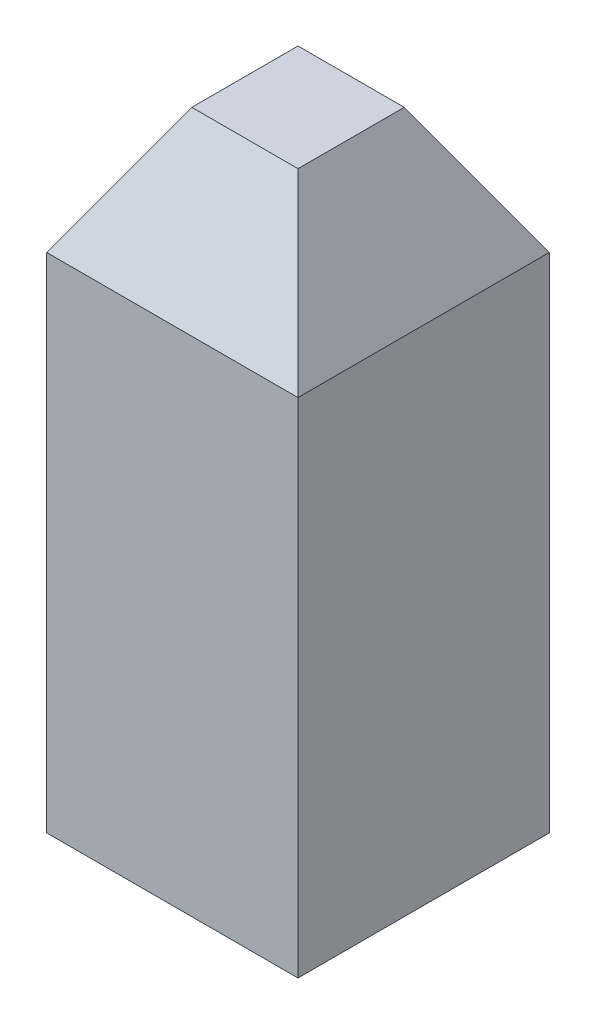
SolidWorks part; units mm, degrees
ref_plane "Front Plane" through (0, 0, 0) normal (0, 0, 1) x (1, 0, 0)
ref_plane "Top Plane" through (0, 0, 0) normal (0, 1, 0) x (1, 0, 0)
ref_plane "Right Plane" through (0, 0, 0) normal (1, 0, 0) x (0, 0, -1)
sketch "Sketch1" plane through (0, 0, 0) normal (0, 1, 0) x (1, 0, 0)
  line L1 (-0.25, -0.25) -> (0.25, -0.25)
  line L2 (-0.25, -0.25) -> (-0.25, 0.25)
  line L3 (-0.25, 0.25) -> (0.25, 0.25)
  line L4 (0.25, -0.25) -> (0.25, 0.25)
  line L5 (-0.25, -0.25) -> (0.25, 0.25) construction
  line L6 (-0.25, 0.25) -> (0.25, -0.25) construction
  point P0 (0, 0)
  dimension "D1" = 0.5
extrude "Boss-Extrude1" add sketch "Sketch1" along normal mid plane 1
sketch "Sketch2" plane through (0, 0.5, 0) normal (0, 1, 0) x (1, 0, 0)
  line L4 (0.25, -0.25) -> (0.25, 0.25)
  line L5 (0.25, 0.25) -> (-0.25, 0.25)
  line L6 (-0.25, 0.25) -> (-0.25, -0.25)
  line L7 (-0.25, -0.25) -> (0.25, -0.25)
  line L8 (0.25, -0.25) -> (0.25, 0.25)
  line L9 (0.25, 0.25) -> (-0.25, 0.25)
  line L10 (-0.25, 0.25) -> (-0.25, -0.25)
  line L11 (-0.25, -0.25) -> (0.25, -0.25)
  dimension "D1" = 0
extrude "Boss-Extrude2" add sketch "Sketch2" along normal blind 0.25 draft 30
